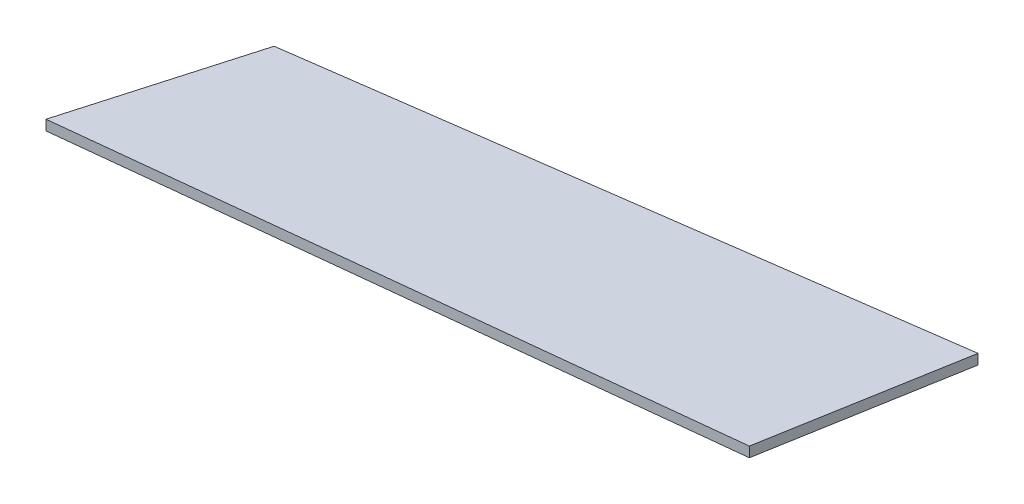
SolidWorks part; units mm, degrees
ref_plane "Plan de face" through (0, 0, 0) normal (0, 0, 1) x (1, 0, 0)
ref_plane "Plan de dessus" through (0, 0, 0) normal (0, 1, 0) x (1, 0, 0)
ref_plane "Plan de droite" through (0, 0, 0) normal (1, 0, 0) x (0, 0, -1)
sketch "Esquisse1" plane through (0, 0, 0) normal (0, 1, 0) x (1, 0, 0)
  line L0 (131.8877, 51.9138) -> (10.0233, 34.9591)
  line L1 (10.0233, 34.9591) -> (0, 0)
  line L2 (0, 0) -> (125.1747, 13.5344)
  line L3 (125.1747, 13.5344) -> (131.8877, 51.9138)
  point P4 (0, 0)
extrude "Boss.-Extru.1" add sketch "Esquisse1" along normal blind 2
